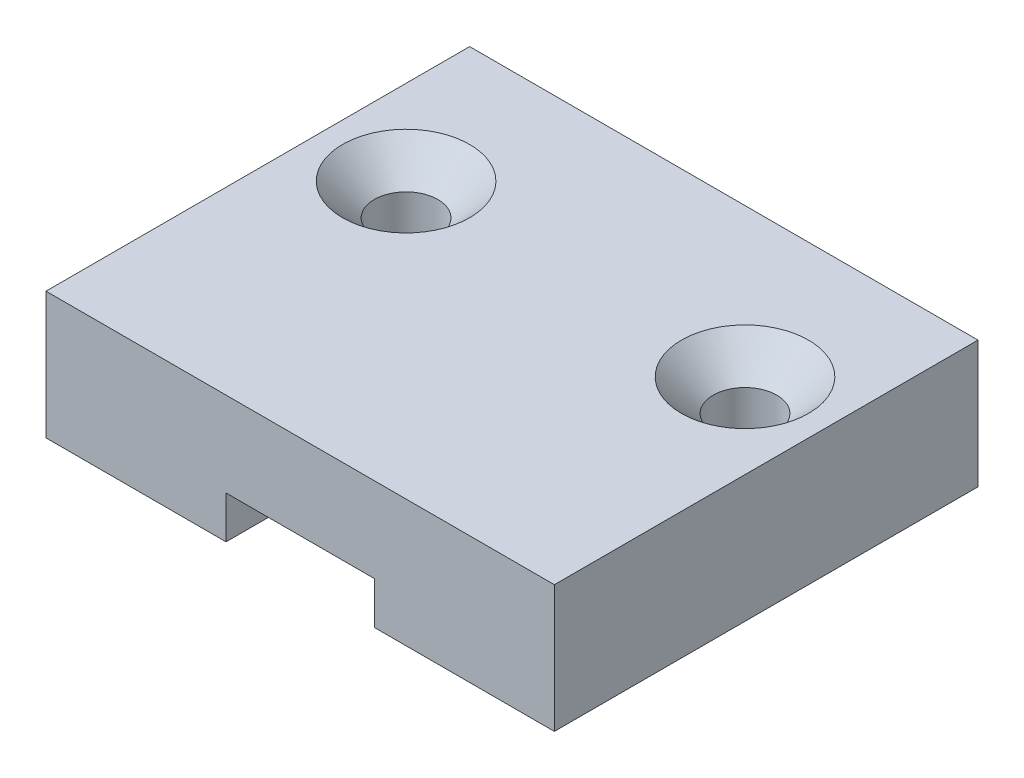
SolidWorks part; units mm, degrees
ref_plane "Plan de face" through (0, 0, 0) normal (0, 0, 1) x (1, 0, 0)
ref_plane "Plan de dessus" through (0, 0, 0) normal (0, 1, 0) x (1, 0, 0)
ref_plane "Plan de droite" through (0, 0, 0) normal (1, 0, 0) x (0, 0, -1)
sketch "Esquisse1" plane through (0, 0, 0) normal (0, 1, 0) x (1, 0, 0)
  line L0 (0, 20) -> (0, 0) construction
  line L1 (-12, 20) -> (12, 20)
  line L2 (-12, 20) -> (-12, 0)
  line L3 (-12, 0) -> (12, 0)
  line L4 (12, 20) -> (12, 0)
  circle A0 centre (8, 13) radius 1.5
  circle A1 centre (-8, 13) radius 1.5
  dimension "D3" = 3
  dimension "D4" = 7
  dimension "D5" = 16
  dimension "D1" = 20
  dimension "D2" = 24
extrude "Boss.-Extru.1" add sketch "Esquisse1" along normal blind 6
sketch "Esquisse2" plane through (0, 0, 0) normal (0, -1, 0) x (1, 0, 0)
  line L0 (3.5, 0) -> (3.5, -2)
  line L1 (-12, 0) -> (12, 0) construction
  line L2 (3.5, -2) -> (7, -2)
  line L3 (7, -2) -> (7, -6)
  line L4 (7, -6) -> (6, -6)
  line L5 (6, -6) -> (6, -20)
  line L6 (12, -20) -> (-12, -20) construction
  line L7 (0, 0) -> (0, -20) construction
  line L8 (-6, -6) -> (-6, -20)
  line L9 (-7, -6) -> (-6, -6)
  line L10 (-7, -2) -> (-7, -6)
  line L11 (-3.5, -2) -> (-7, -2)
  line L12 (-3.5, 0) -> (-3.5, -2)
  line L13 (-3.5, 0) -> (3.5, 0)
  line L14 (-6, -20) -> (6, -20)
  dimension "D1" = 14
  dimension "D2" = 4
  dimension "D3" = 2
  dimension "D4" = 12
  dimension "D5" = 7
extrude "Enlèv. mat.-Extru.1" cut sketch "Esquisse2" against normal blind 2
chamfer "Chanfrein1" distance 1.5 angle 45 2 edges at (8, 6, -11.5) (-8, 6, -14.5)
